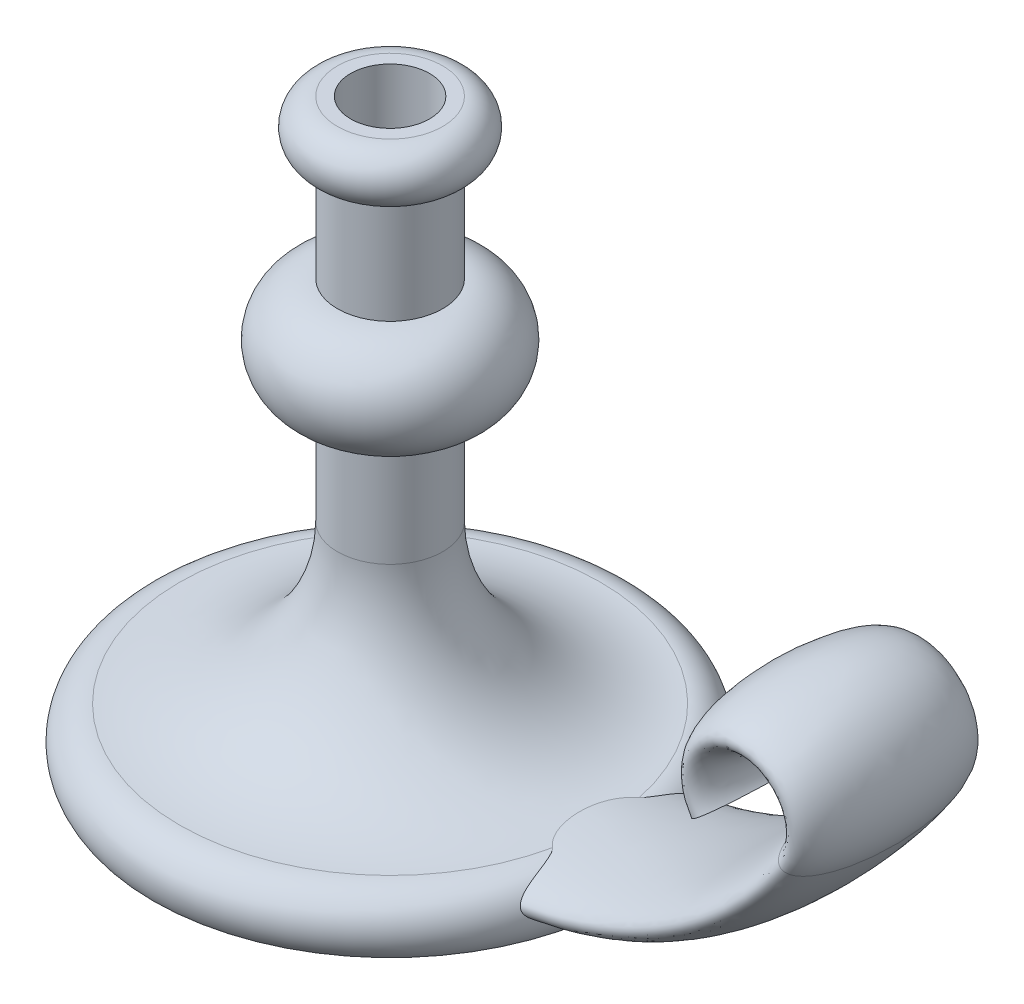
SolidWorks part; units mm, degrees
ref_plane "Front Plane" through (0, 0, 0) normal (0, 0, 1) x (1, 0, 0)
ref_plane "Top Plane" through (0, 0, 0) normal (0, 1, 0) x (1, 0, 0)
ref_plane "Right Plane" through (0, 0, 0) normal (1, 0, 0) x (0, 0, -1)
sketch "Sketch1" plane through (0, 0, 0) normal (0, 0, 1) x (1, 0, 0)
  line L0 (0, 127.4954) -> (0, -92.5046)
  line L1 (0, 127.4954) -> (20, 127.4954)
  line L2 (0, -92.5046) -> (90, -92.5046)
  line L4 (20, 107.4954) -> (20, 67.4954)
  line L5 (20, 27.4954) -> (20, -12.5046)
  arc A0 (20, 107.4954) -> (20, 127.4954) centre (20, 117.4954) ccw
  arc A1 (20, 67.4954) -> (20, 27.4954) centre (20, 47.4954) cw
  arc A2 (20, -12.5046) -> (80, -72.5046) centre (80, -12.5046) ccw
  arc A3 (80, -72.5046) -> (90, -92.5046) centre (80, -85.0046) cw
  dimension "D6" = 20
  dimension "D9" = 60
  dimension "D1" = 220
  dimension "D2" = 20
  dimension "D3" = 90
  dimension "D4" = 20
  dimension "D5" = 12.5
  dimension "D7" = 40
  dimension "D8" = 80
revolve "Revolve1" add sketch "Sketch1" angle 360 about L0
sketch "Sketch2" plane through (0, 0, 0) normal (0, 0, 1) x (1, 0, 0)
  line L0 (0, 23.4954) -> (0, 95.4954) construction
  line L1 (0, -82.5046) -> (60, -82.5046)
  line L2 (-90, -92.5046) -> (90, -92.5046) construction
  arc A0 (60, -82.5046) -> (183.5921, -17.5046) centre (60, 67.4954) ccw
  arc A1 (183.5921, -17.5046) -> (150.6342, -17.5046) centre (167.1131, -6.1713) ccw
  dimension "D2" = 150
  dimension "D4" = 20
  dimension "D1" = 60
  dimension "D3" = 65
  dimension "D5" = 10
sketch "Sketch3" plane through (0, 0, 0) normal (1, 0, 0) x (0, 0, -1)
  ellipse E0 centre (0, -82.5046) end of major axis (35, -82.5046) minor radius 10
sweep "Sweep1" add profiles "Sketch3" path "Sketch2"
sketch "Sketch7" plane through (0, 127.4954, 0) normal (0, 1, 0) x (1, 0, 0)
  circle A0 centre (0, 0) radius 15
  dimension "D1" = 30
extrude "Cut-Extrude1" cut sketch "Sketch7" against normal blind 25 contours A0
